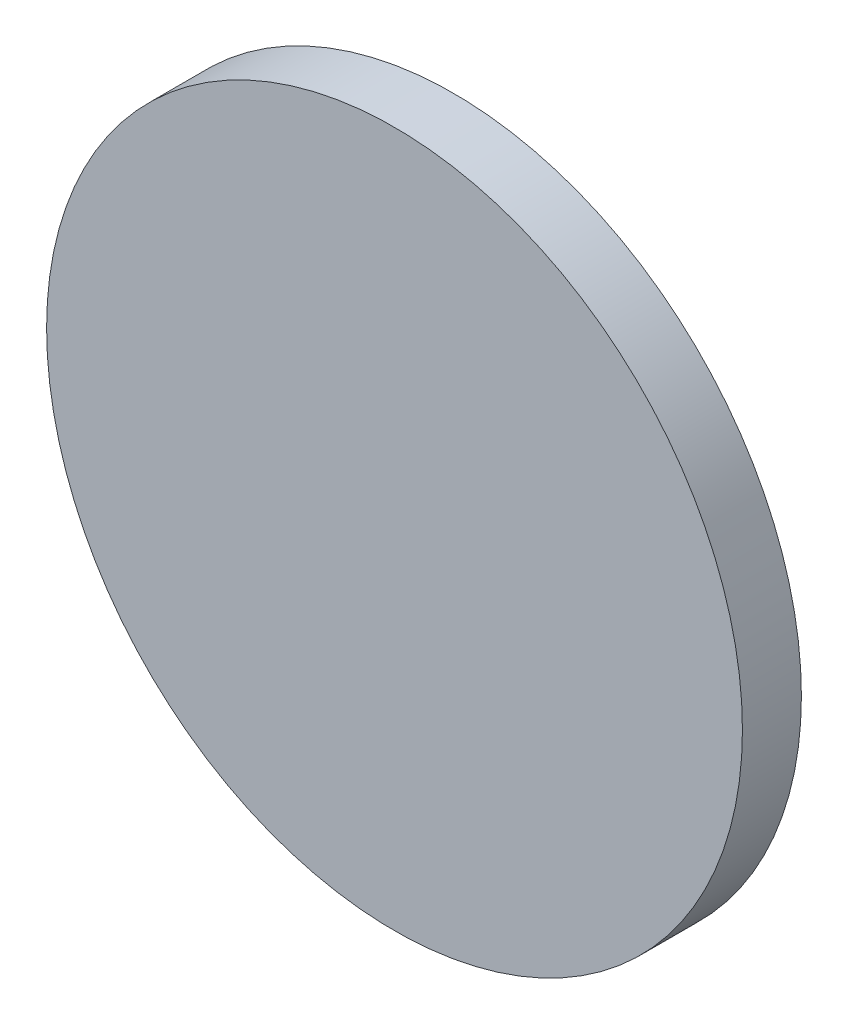
SolidWorks part; units mm, degrees
ref_plane "Front Plane" through (0, 0, 0) normal (0, 0, 1) x (1, 0, 0)
ref_plane "Top Plane" through (0, 0, 0) normal (0, 1, 0) x (1, 0, 0)
ref_plane "Right Plane" through (0, 0, 0) normal (1, 0, 0) x (0, 0, -1)
sketch "Sketch2" plane through (0, 0, 0) normal (0, 0, 1) x (1, 0, 0)
  circle A0 centre (0, 0) radius 29.5
  dimension "D1" = 59
extrude "Boss-Extrude1" add sketch "Sketch2" along normal blind 60
ref_plane "Plane1" through (0, 0, 55) normal (0, 0, 1) x (1, 0, 0)
sketch "Sketch4" plane through (0, 0, 55) normal (0, 0, 1) x (1, 0, 0)
  line L0 (-16.25, 0) -> (16.25, 0)
  line L1 (0, 9.3175) -> (0, -9.8919) construction
  arc A0 (-16.25, 0) -> (16.25, 0) centre (0, 0) cw
  point P6 (0, 0)
  dimension "D1" = 32.5
revolve "Cut-Revolve1" cut sketch "Sketch4" angle 180 about L0
ref_plane "Plane2" through (0, 0, 50) normal (0, 0, 1) x (1, 0, 0)
sketch "Sketch5" plane through (0, 0, 50) normal (0, 0, 1) x (1, 0, 0)
  line L1 (-44.67, 42.2843) -> (47.0988, 42.2843)
  line L2 (-44.67, 42.2843) -> (-44.67, -46.4708)
  line L3 (-44.67, -46.4708) -> (47.0988, -46.4708)
  line L4 (47.0988, 42.2843) -> (47.0988, -46.4708)
extrude "Cut-Extrude1" cut sketch "Sketch5" along normal up to next
sketch "Sketch6" plane through (0, 0, 0) normal (0, 0, -1) x (-1, 0, 0)
  circle A0 centre (0, 0) radius 10.1
  dimension "D1" = 20.2
extrude "Cut-Extrude2" cut sketch "Sketch6" against normal blind 2
sketch "Sketch7" plane through (0, 0, 50) normal (0, 0, 1) x (1, 0, 0)
  line L1 (-31.4741, 33.4815) -> (32.8085, 33.4815)
  line L2 (-31.4741, 33.4815) -> (-31.4741, -32.2196)
  line L3 (-31.4741, -32.2196) -> (32.8085, -32.2196)
  line L4 (32.8085, 33.4815) -> (32.8085, -32.2196)
extrude "Cut-Extrude3" cut sketch "Sketch7" against normal blind 45
